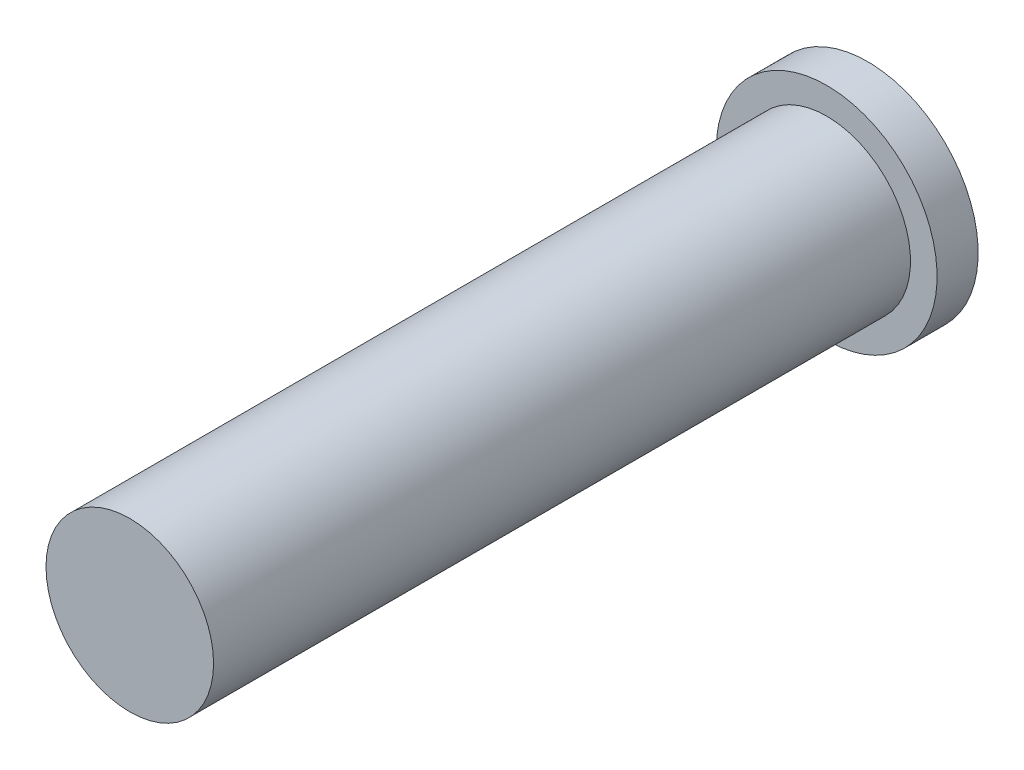
SolidWorks part; units mm, degrees
ref_plane "Front Plane" through (0, 0, 0) normal (0, 0, 1) x (1, 0, 0)
ref_plane "Top Plane" through (0, 0, 0) normal (0, 1, 0) x (1, 0, 0)
ref_plane "Right Plane" through (0, 0, 0) normal (1, 0, 0) x (0, 0, -1)
sketch "Sketch1" plane through (0, 0, 0) normal (0, 0, 1) x (1, 0, 0)
  circle A0 centre (0, 0) radius 0.755
extrude "Boss-Extrude1" add sketch "Sketch1" along normal blind 6.28
sketch "Sketch2" plane through (0, 0, 0) normal (0, 0, -1) x (-1, 0, 0)
  circle A0 centre (0, 0) radius 0.995
extrude "Boss-Extrude2" add sketch "Sketch2" along normal blind 0.37
sketch "Sketch3" plane through (0, 0, -0.37) normal (0, 0, -1) x (-1, 0, 0)
  circle A0 centre (0, 0) radius 0.58
extrude "Cut-Extrude1" cut sketch "Sketch3" against normal blind 6
